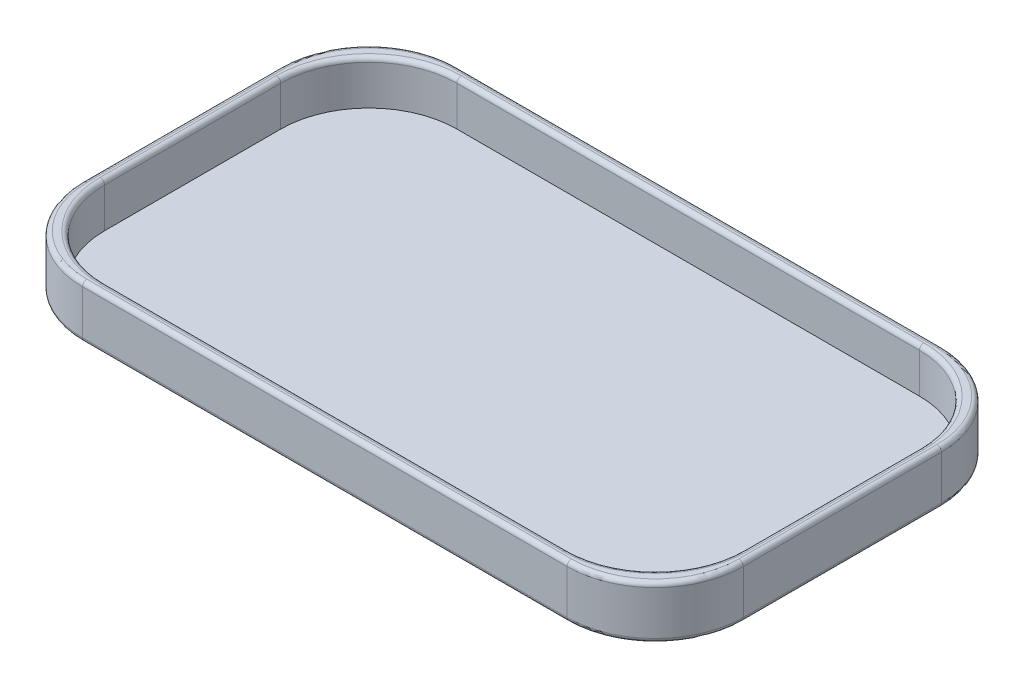
SolidWorks part; units mm, degrees
ref_plane "Front Plane" through (0, 0, 0) normal (0, 0, 1) x (1, 0, 0)
ref_plane "Top Plane" through (0, 0, 0) normal (0, 1, 0) x (1, 0, 0)
ref_plane "Right Plane" through (0, 0, 0) normal (1, 0, 0) x (0, 0, -1)
sketch "Sketch1" plane through (0, 0, 0) normal (0, 1, 0) x (1, 0, 0)
  line L1 (-75, -42.5) -> (75, -42.5)
  line L2 (-75, -42.5) -> (-75, 42.5)
  line L3 (-75, 42.5) -> (75, 42.5)
  line L4 (75, -42.5) -> (75, 42.5)
  line L5 (-75, -42.5) -> (75, 42.5) construction
  line L6 (-75, 42.5) -> (75, -42.5) construction
  point P0 (0, 0)
  dimension "D1" = 150
  dimension "D2" = 85
extrude "Boss-Extrude1" add sketch "Sketch1" along normal blind 2
sketch "Sketch2" plane through (0, 2, 0) normal (0, 1, 0) x (1, 0, 0)
  line L1 (-75, -42.5) -> (75, -42.5)
  line L2 (-75, -42.5) -> (-75, 42.5)
  line L3 (-75, 42.5) -> (75, 42.5)
  line L4 (75, -42.5) -> (75, 42.5)
  line L5 (-75, -42.5) -> (75, 42.5) construction
  line L6 (-75, 42.5) -> (75, -42.5) construction
  line L7 (-72.5, -40) -> (72.5, -40)
  line L8 (-72.5, -40) -> (-72.5, 40)
  line L9 (-72.5, 40) -> (72.5, 40)
  line L10 (72.5, -40) -> (72.5, 40)
  line L11 (-72.5, -40) -> (72.5, 40) construction
  line L12 (-72.5, 40) -> (72.5, -40) construction
  point P0 (0, 0)
  point P7 (0, 0)
  dimension "D1" = 145
  dimension "D2" = 80
extrude "Boss-Extrude2" add sketch "Sketch2" along normal blind 10
fillet "Fillet1" radius 20 8 edges at (75, 6, -42.5) (75, 6, 42.5) (-75, 6, 42.5) (-75, 6, -42.5) (-72.5, 7, 40) (72.5, 7, 40) (72.5, 7, -40) (-72.5, 7, -40)
fillet "Fillet2" radius 1 24 edges at (-69.1421, 0, -36.6421) (-75, 0, 0) (-69.1421, 0, 36.6421) (0, 0, 42.5) (69.1421, 0, 36.6421) (75, 0, 0) (69.1421, 0, -36.6421) (0, 0, -42.5) (66.6421, 12, -34.1421) (0, 12, -40) (-66.6421, 12, -34.1421) (-72.5, 12, 0) (-66.6421, 12, 34.1421) (0, 12, 40) (66.6421, 12, 34.1421) (72.5, 12, 0) (69.1421, 12, 36.6421) (0, 12, 42.5) (-69.1421, 12, 36.6421) (-75, 12, 0) (-69.1421, 12, -36.6421) (0, 12, -42.5) (69.1421, 12, -36.6421) (75, 12, 0)
